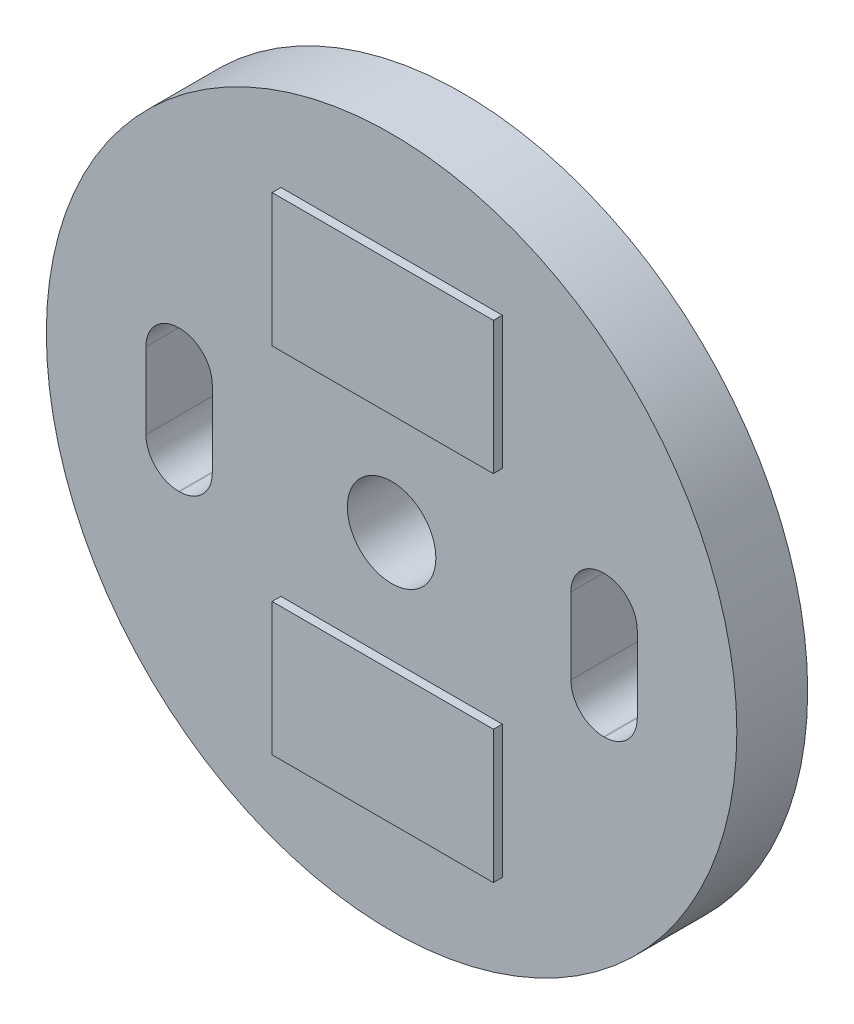
SolidWorks part; units mm, degrees
ref_plane "Front" through (0, 0, 0) normal (0, 0, 1) x (1, 0, 0)
ref_plane "Top" through (0, 0, 0) normal (0, 1, 0) x (1, 0, 0)
ref_plane "Right" through (0, 0, 0) normal (1, 0, 0) x (0, 0, -1)
sketch "草图1" plane through (0, 0, 0) normal (0, 0, 1) x (1, 0, 0)
  line L1 (-2.405, 0.8) -> (-2.395, 0.8)
  line L2 (-2.775, 0.43) -> (-2.775, -0.43)
  line L3 (-2.405, -0.8) -> (-2.395, -0.8)
  line L4 (-2.025, 0.43) -> (-2.025, -0.43)
  line L5 (2.395, 0.8) -> (2.405, 0.8)
  line L6 (2.025, 0.43) -> (2.025, -0.43)
  line L7 (2.395, -0.8) -> (2.405, -0.8)
  line L8 (2.775, 0.43) -> (2.775, -0.43)
  circle A0 centre (0, 0) radius 3.9
  circle A1 centre (0, 0) radius 0.5
  arc A2 (2.405, -0.8) -> (2.775, -0.43) centre (2.405, -0.43) ccw
  arc A3 (2.025, -0.43) -> (2.395, -0.8) centre (2.395, -0.43) ccw
  arc A4 (2.405, 0.8) -> (2.775, 0.43) centre (2.405, 0.43) cw
  arc A5 (2.395, 0.8) -> (2.025, 0.43) centre (2.395, 0.43) ccw
  arc A6 (-2.405, 0.8) -> (-2.775, 0.43) centre (-2.405, 0.43) ccw
  arc A7 (-2.775, -0.43) -> (-2.405, -0.8) centre (-2.405, -0.43) ccw
  arc A8 (-2.395, -0.8) -> (-2.025, -0.43) centre (-2.395, -0.43) ccw
  arc A9 (-2.395, 0.8) -> (-2.025, 0.43) centre (-2.395, 0.43) cw
  point P12 (-2.025, 0)
  point P13 (2.025, 0)
  point P14 (-2.4, 0.8)
  point P15 (2.4, 0.8)
  point P18 (2.775, -0.8)
  point P21 (2.025, -0.8)
  point P24 (2.775, 0.8)
  point P29 (-2.775, 0.8)
  point P32 (-2.775, -0.8)
  point P35 (-2.025, -0.8)
  dimension "D1" = 7.8
  dimension "D10" = 0.37
  dimension "D11" = 1
  dimension "D2" = 0
  dimension "D3" = 0
  dimension "D4" = 2.4
  dimension "D5" = 2.4
  dimension "D6" = 0.75
  dimension "D7" = 0.75
  dimension "D8" = 1.6
  dimension "D9" = 1.6
extrude "凸台-拉伸1" add sketch "草图1" along normal blind 0.8
sketch "草图2" plane through (0, 0, 0.8) normal (0, 0, 1) x (1, 0, 0)
  line L1 (-1.25, 2.75) -> (1.25, 2.75)
  line L2 (-1.25, 2.75) -> (-1.25, 1.25)
  line L3 (-1.25, 1.25) -> (1.25, 1.25)
  line L4 (1.25, 2.75) -> (1.25, 1.25)
  line L5 (-1.25, -1.25) -> (1.25, -1.25)
  line L6 (-1.25, -1.25) -> (-1.25, -2.75)
  line L7 (-1.25, -2.75) -> (1.25, -2.75)
  line L8 (1.25, -1.25) -> (1.25, -2.75)
  point P8 (0, 1.25)
  point P10 (1.25, 2)
  point P11 (-1.25, -2)
  point P12 (0, -1.25)
  dimension "D1" = 2.5
  dimension "D2" = 0
  dimension "D3" = 1.5
  dimension "D4" = 2
  dimension "D5" = 1.5
  dimension "D6" = 2.5
  dimension "D7" = 2
  dimension "D8" = 0
extrude "凸台-拉伸2" add sketch "草图2" along normal blind 0.1
